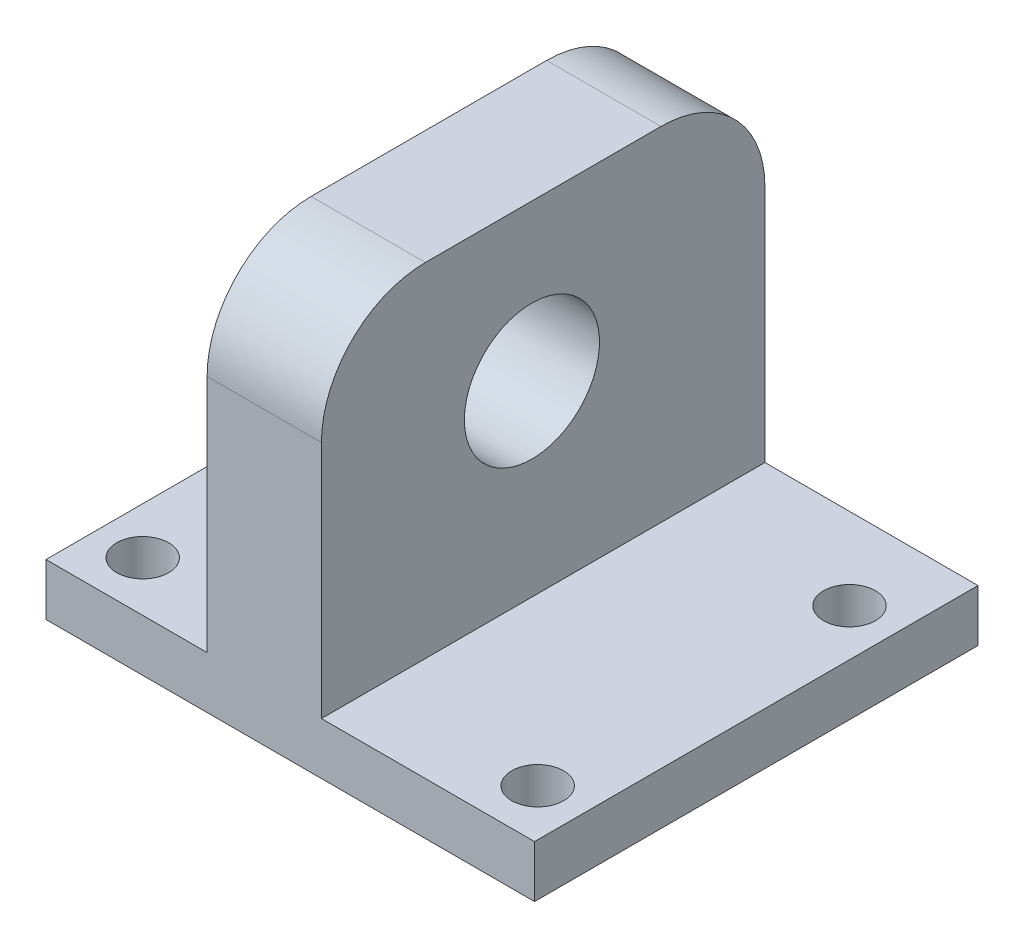
SolidWorks part; units mm, degrees
ref_plane "前视基准面" through (0, 0, 0) normal (0, 0, 1) x (1, 0, 0)
ref_plane "上视基准面" through (0, 0, 0) normal (0, 1, 0) x (1, 0, 0)
ref_plane "右视基准面" through (0, 0, 0) normal (1, 0, 0) x (0, 0, -1)
other "Configuration Table"
sketch "草图1" plane through (0, 0, 0) normal (0, 1, 0) x (1, 0, 0)
  line L1 (23.5, -12.9607) -> (-23.5, -12.9607)
  line L2 (23.5, -12.9607) -> (23.5, 29.7046)
  line L3 (23.5, 29.7046) -> (-23.5, 29.7046)
  line L4 (-23.5, -12.9607) -> (-23.5, 29.7046)
  circle A0 centre (-19, 21.8424) radius 2.5
  circle A1 centre (19, 21.8424) radius 2.5
  circle A2 centre (-19, -8.1576) radius 2.5
  circle A3 centre (19, -8.1576) radius 2.5
  point P0 (0, 0)
  dimension "D2" = 5
  dimension "D3" = 5
  dimension "D4" = 5
  dimension "D5" = 5
  dimension "D1" = 47
  dimension "D6" = 7.8621
extrude "凸台-拉伸1" add sketch "草图1" along normal blind 5 contours L4 L1 L2 L3 A3 A2 A1 A0
sketch "草图2" plane through (0, 5, 0) normal (0, 1, 0) x (1, 0, 0)
  line L0 (23.5, 29.7046) -> (-23.5, 29.7046) construction
  line L1 (3, -12.9607) -> (-3, -12.9607)
  line L2 (3, -12.9607) -> (3, 29.7046)
  line L3 (3, 29.7046) -> (-3, 29.7046)
  line L4 (-3, -12.9607) -> (-3, 29.7046)
  line L5 (3, -12.9607) -> (-3, 29.7046) construction
  line L6 (3, 29.7046) -> (-3, -12.9607) construction
  line L7 (23.5, -12.9607) -> (-23.5, -12.9607) construction
  line L8 (0, 8.3719) -> (0, 0)
  line L9 (23.5, -12.9607) -> (23.5, 29.7046) construction
  line L10 (-23.5, 29.7046) -> (23.5, 29.7046)
  line L11 (-23.5, 29.7046) -> (-23.5, 27.7046)
  line L12 (-23.5, 27.7046) -> (23.5, 27.7046)
  line L13 (23.5, 29.7046) -> (23.5, 27.7046)
  point P0 (0, 8.3719)
  dimension "D1" = 6
  dimension "D2" = 2
extrude "凸台-拉伸2" add sketch "草图2" along normal blind 33
sketch "草图3" plane through (-3, 0, 0) normal (-1, 0, 0) x (0, 0, 1)
  line L0 (-27.7046, 5) -> (12.9607, 5)
extrude "凸台-拉伸3" add sketch "草图3" against normal up to surface (6 mm away) up to face at (3, 21.5, -7.3719)
sketch "草图4" plane through (-3, 2.1172, 0) normal (-1, 0, 0) x (0, 0, 1)
  line L12 (-27.6221, 2.1767) -> (13.0432, 2.1767)
  line L13 (13.0432, 2.1767) -> (13.0432, 20.1767)
  line L16 (-29.6221, 20.1767) -> (-27.6221, 20.1767)
  line L17 (-27.6221, 20.1767) -> (-27.6221, 2.1767)
  line L18 (13.0432, 20.1767) -> (-2.9362, 26.9857)
  line L21 (-10.6523, 27.5823) -> (-29.6221, 20.1767)
  circle A0 centre (-7.2895, 20.8784) radius 6.5
  arc A5 (-2.9362, 26.9857) -> (-10.6523, 27.5823) centre (-7.2895, 20.8784) ccw
  dimension "D2" = 13
extrude "切除-拉伸2" cut sketch "草图4" against normal blind 7 contours A0
chamfer "倒角1" distance 3 angle 45 2 edges at (23.5, 38, -28.7046) (-23.5, 38, -28.7046)
sketch "草图6" plane through (0, 38, 0) normal (0, 1, 0) x (1, 0, 0)
  line L0 (-3, 21.5525) -> (28.9873, 21.5525)
  line L1 (-3, -12.9607) -> (-3, 27.7046) construction
  line L2 (28.9873, 21.5525) -> (28.9873, 31.4157)
  line L3 (28.9873, 31.4157) -> (-26.3946, 31.4157)
  line L4 (-26.3946, 31.4157) -> (-26.3946, 21.5525)
  line L5 (-26.3946, 21.5525) -> (-3, 21.5525)
  line L10 (-26.3946, 22.2925) -> (28.9873, 22.2925)
  line L11 (-26.3946, 22.2925) -> (-26.3946, 21.5525)
  line M6 (3, 27.7046) -> (20.5, 27.7046)
  line M7 (20.5, 27.7046) -> (20.5, 29.7046)
  line M8 (20.5, 29.7046) -> (-20.5, 29.7046)
  line M9 (-20.5, 29.7046) -> (-20.5, 27.7046)
  line M10 (-20.5, 27.7046) -> (-3, 27.7046)
  line M11 (-3, 27.7046) -> (-3, -12.9607)
  line M13 (3, -12.9607) -> (3, 27.7046)
  dimension "D1" = 0.74
extrude "切除-拉伸8" cut sketch "草图6" against normal blind 25 contours L4 L10 L2 L3 M11 M10 M9 M8 M7 M6 M13 | L10 M11 M13 M6 M7 M8 M9 M10
sketch "草图7" plane through (0, 0, -27.7046) normal (0, 0, 1) x (1, 0, 0)
  line L4 (23.5, 13) -> (3, 13)
  line L5 (3, 13) -> (3, 5)
  line L6 (3, 5) -> (23.5, 5)
  line L7 (23.5, 5) -> (23.5, 13)
  line L8 (23.5, 13) -> (3, 13)
  line L9 (3, 13) -> (3, 5)
  line L10 (3, 5) -> (23.5, 5)
  line L11 (23.5, 5) -> (23.5, 13)
  dimension "D1" = 0
extrude "切除-拉伸9" cut sketch "草图7" against normal blind 10
sketch "草图8" plane through (-3, 0, 0) normal (-1, 0, 0) x (0, 0, 1)
  line L6 (12.9607, 38) -> (-22.2925, 38)
  line L7 (12.9607, 38) -> (-22.2925, 38)
  line L10 (-22.2925, 38) -> (-22.2925, 13)
  line L11 (-22.2925, 13) -> (-27.7046, 13)
  line L12 (-27.7046, 13) -> (-27.7046, 5)
  line L13 (-27.7046, 5) -> (12.9607, 5)
  line L14 (12.9607, 5) -> (12.9607, 38)
  line L18 (-22.2925, 38) -> (-22.2925, 13)
  line L19 (-22.2925, 13) -> (-27.7046, 13)
  line L20 (-27.7046, 13) -> (-27.7046, 5)
  line L21 (-27.7046, 5) -> (12.9607, 5)
  line L22 (12.9607, 5) -> (12.9607, 38)
  circle A0 centre (-7.2895, 22.9956) radius 6.5 construction
  circle A1 centre (-7.2895, 22.9956) radius 6.5
  dimension "D1" = 0
extrude "凸台-拉伸4" add sketch "草图8" along normal blind 5
fillet "圆角4" radius 2 1 edges at (-8, 9, -27.7046)
sketch "草图9" plane through (0, 13, 0) normal (0, 1, 0) x (1, 0, 0)
  line L1 (-8, 22.2925) -> (3, 22.2925)
  line L2 (-8, 22.2925) -> (-8, 29.7046)
  line L3 (-8, 29.7046) -> (3, 29.7046)
  line L4 (3, 22.2925) -> (3, 29.7046)
extrude "凸台-拉伸5" add sketch "草图9" along normal blind 25
fillet "圆角5" radius 10 2 edges at (-2.5, 38, -29.7046) (-2.5, 38, 12.9607)
sketch "草图10" plane through (0, 0, -29.7046) normal (0, 0, -1) x (-1, 0, 0)
  line L0 (2.5, 28) -> (2.5, 0.6188)
  line L1 (8, 28) -> (-3, 28) construction
  line L4 (23.5, 9) -> (2.5, 9)
  line L7 (10, 5) -> (23.5, 5)
  line L8 (10, 13) -> (10, 5)
  line L9 (23.5, 13) -> (10, 13)
  line L10 (23.5, 5) -> (23.5, 13)
  line L11 (10, 5) -> (23.5, 5)
  line L12 (10, 13) -> (10, 5)
  line L13 (23.5, 13) -> (10, 13)
  line L14 (23.5, 5) -> (23.5, 13)
  circle A0 centre (2.5, 14.3094) radius 2
  circle A1 centre (16.6032, 9) radius 2
  dimension "D1" = 4
  dimension "D3" = 4
  dimension "D2" = 0
extrude "切除-拉伸10" cut sketch "草图10" against normal blind 4 contours L4 A1 | L4 A1 | L0 A0 | L0 A0
